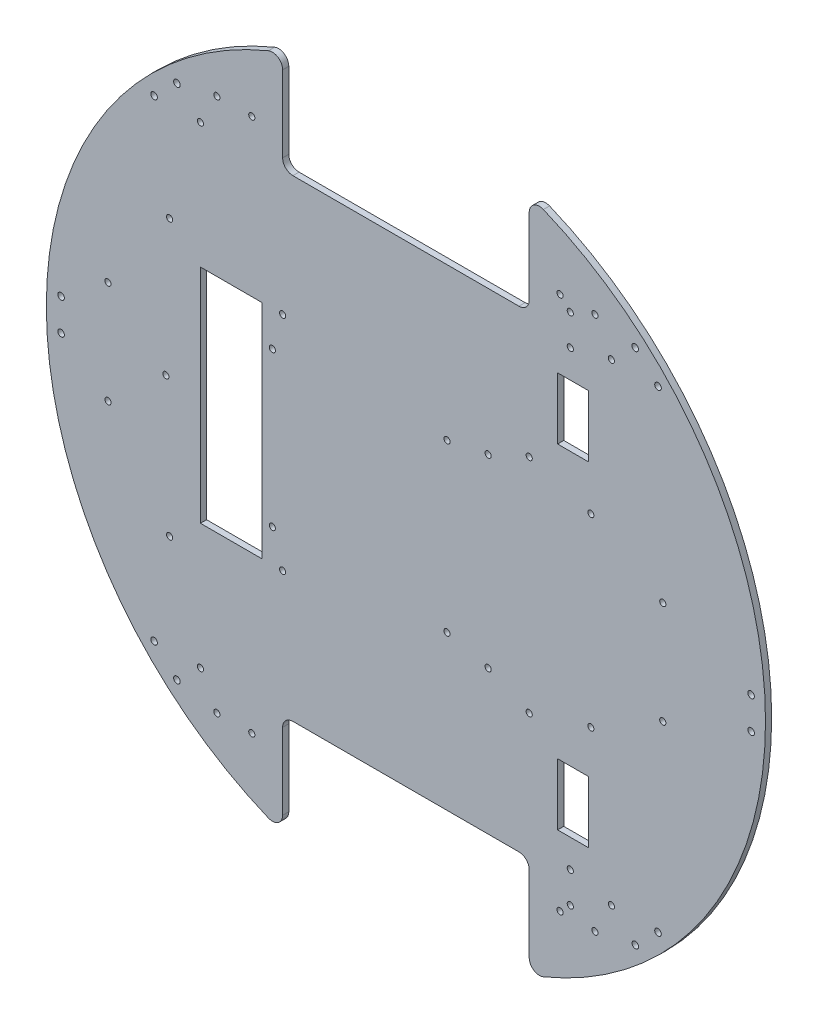
SolidWorks part; units mm, degrees
material "ｱｸﾘﾙ (中-上級の耐衝撃性)"
ref_plane "正面" through (0, 0, 0) normal (0, 0, 1) x (1, 0, 0)
ref_plane "平面" through (0, 0, 0) normal (0, 1, 0) x (1, 0, 0)
ref_plane "右側面" through (0, 0, 0) normal (1, 0, 0) x (0, 0, -1)
sketch "ｽｹｯﾁ1" plane through (0, 0, 0) normal (0, 0, 1) x (1, 0, 0)
  circle A0 centre (0, 0) radius 175
  dimension "D1" = 350
extrude "ﾎﾞｽ - 押し出し1" add sketch "ｽｹｯﾁ1" along normal blind 3
sketch "ｽｹｯﾁ2" plane through (0, 0, 3) normal (0, 0, 1) x (1, 0, 0)
  line L0 (0, 0) -> (175, 0)
  line L1 (0, 0) -> (-175, 0)
  line L2 (0, 0) -> (0, 115)
  line L3 (0, 0) -> (0, -115)
  line L4 (0, 115) -> (60, 115)
  line L5 (0, 115) -> (0, 175)
  line L6 (0, 175) -> (60, 175)
  line L7 (60, 115) -> (60, 175)
  line L8 (0, 115) -> (-60, 115)
  line L9 (0, 115) -> (0, 175)
  line L10 (0, 175) -> (-60, 175)
  line L11 (-60, 115) -> (-60, 175)
  line L13 (0, -115) -> (60, -115)
  line L14 (0, -115) -> (0, -175)
  line L15 (0, -175) -> (60, -175)
  line L16 (60, -115) -> (60, -175)
  line L17 (0, -115) -> (-60, -115)
  line L18 (0, -115) -> (0, -175)
  line L19 (0, -175) -> (-60, -175)
  line L20 (-60, -115) -> (-60, -175)
  circle A0 centre (0, 0) radius 175 construction
  circle M1 centre (0, 0) radius 175
  dimension "D1" = 115
  dimension "D2" = 60
  dimension "D3" = 60
  dimension "D4" = 60
  dimension "D5" = 115
  dimension "D6" = 60
extrude "ｶｯﾄ - 押し出し1" cut sketch "ｽｹｯﾁ2" against normal blind 3 contours L11 L8 L5 M1 | L4 L7 L5 M1 | L17 L20 L14 M1 | L16 L13 L14 M1
fillet "ﾌｨﾚｯﾄ1" radius 5 1 edges at (-60, 164.3928, 1.5)
fillet "ﾌｨﾚｯﾄ2" radius 5 3 edges at (60, 115, 1.5) (60, 164.3928, 1.5) (-60, 115, 1.5)
fillet "ﾌｨﾚｯﾄ3" radius 5 4 edges at (-60, -164.3928, 1.5) (-60, -115, 1.5) (60, -164.3928, 1.5) (60, -115, 1.5)
sketch "ｽｹｯﾁ5" plane through (0, 0, 3) normal (0, 0, 1) x (1, 0, 0)
  line L0 (0, 115) -> (-100, 115)
  line L1 (55, 115) -> (-55, 115) construction
  line L2 (0, 115) -> (100, 115)
  line L3 (0, -115) -> (100, -115)
  line L4 (55, -115) -> (-55, -115) construction
  line L5 (100, -115) -> (-100, -115)
  circle A0 centre (-100, -115) radius 1.5
  circle A1 centre (100, -115) radius 1.5
  circle A2 centre (100, 115) radius 1.5
  circle A3 centre (-100, 115) radius 1.5
  dimension "D3" = 3
  dimension "D4" = 3
  dimension "D5" = 3
  dimension "D6" = 3
  dimension "D1" = 100
  dimension "D2" = 100
extrude "ｶｯﾄ - 押し出し4" cut sketch "ｽｹｯﾁ5" against normal blind 3 contours A1 | A0 | A3 | A2
sketch "ｽｹｯﾁ6" plane through (0, 0, 3) normal (0, 0, 1) x (1, 0, 0)
  line L1 (-60, 54) -> (60, 54)
  line L2 (-60, 54) -> (-60, -54)
  line L3 (-60, -54) -> (60, -54)
  line L4 (60, 54) -> (60, -54)
  line L5 (-60, 54) -> (60, -54) construction
  line L6 (-60, -54) -> (60, 54) construction
  circle A0 centre (-60, 54) radius 1.5
  circle A1 centre (60, 54) radius 1.5
  circle A2 centre (-60, -54) radius 1.5
  circle A3 centre (60, -54) radius 1.5
  point P0 (0, 0)
  dimension "D3" = 3
  dimension "D4" = 3
  dimension "D5" = 3
  dimension "D6" = 3
  dimension "D1" = 120
  dimension "D2" = 108
extrude "ｶｯﾄ - 押し出し5" cut sketch "ｽｹｯﾁ6" against normal blind 3 contours A2 | A0 | A1 | A3
sketch "ｽｹｯﾁ7" plane through (0, 0, 3) normal (0, 0, 1) x (1, 0, 0)
  line L0 (-60, -54) -> (-70, -54)
  line L2 (-70, -54) -> (-100, -54)
  line L3 (-70, -54) -> (-70, 54)
  line L4 (-70, 54) -> (-100, 54)
  line L5 (-100, -54) -> (-100, 54)
  dimension "D1" = 10
  dimension "D2" = 108
  dimension "D3" = 30
extrude "ｶｯﾄ - 押し出し6" cut sketch "ｽｹｯﾁ7" against normal blind 3 contours L5 L2 L3 L4
sketch "ｽｹｯﾁ8" plane through (0, 0, 3) normal (0, 0, 1) x (1, 0, 0)
  line L0 (-100, 0) -> (-115, 0)
  line L1 (-100, -54) -> (-100, 54) construction
  line L2 (-115, 0) -> (-115, 67)
  line L3 (-115, 0) -> (-115, -67)
  circle A0 centre (-115, -67) radius 1.5
  circle A1 centre (-116.8225, 0) radius 1.5
  circle A2 centre (-115, 67) radius 1.5
  dimension "D4" = 3
  dimension "D5" = 3
  dimension "D6" = 3
  dimension "D1" = 15
  dimension "D2" = 67
  dimension "D3" = 67
extrude "ｶｯﾄ - 押し出し7" cut sketch "ｽｹｯﾁ8" against normal blind 3 contours A2 | A1 | A0
sketch "ｽｹｯﾁ9" plane through (0, 0, 3) normal (0, 0, 1) x (1, 0, 0)
  line L0 (-70, 0) -> (-65, 0)
  line L1 (-70, -54) -> (-70, 54) construction
  line L2 (-65, 0) -> (-65, 37)
  line L3 (-65, 37) -> (-64.7716, 37.1905)
  line L4 (-65, 0) -> (-65, -38)
  line L5 (-65, 0) -> (20, 0)
  line L6 (20, 0) -> (20, 41)
  line L7 (20, 0) -> (20, -40)
  circle A0 centre (-65, 37) radius 1.5
  circle A1 centre (20, 41) radius 1.5
  circle A2 centre (-65, -38) radius 1.5
  circle A3 centre (20, -40) radius 1.5
  dimension "D7" = 3
  dimension "D8" = 3
  dimension "D9" = 3
  dimension "D10" = 3
  dimension "D1" = 5
  dimension "D2" = 37
  dimension "D3" = 38
  dimension "D4" = 85
  dimension "D5" = 41
  dimension "D6" = 40
extrude "ｶｯﾄ - 押し出し8" cut sketch "ｽｹｯﾁ9" against normal blind 10 contours A0 | A2 | A1 | A3
sketch "ｽｹｯﾁ10" plane through (0, 0, 3) normal (0, 0, 1) x (1, 0, 0)
  line L0 (0, 0) -> (152.2366, 0)
  line L1 (0, 0) -> (66.9742, 68.8711)
  line L2 (0, 0) -> (76.2283, -78.3873)
  line L3 (175, 0) -> (168, 0)
  line L4 (-175, 0) -> (-168, 0)
  line L5 (66.9742, 68.8711) -> (117.1237, 120.441)
  line L6 (76.2283, -78.3873) -> (117.1237, -120.441)
  line L7 (117.1237, -120.441) -> (122.6798, -115.038)
  line L8 (117.1237, -120.441) -> (111.6437, -125.9211)
  line L9 (168, 0) -> (168, 7.75)
  line L10 (168, 0) -> (168, -7.75)
  line L11 (117.1237, 120.441) -> (111.5677, 125.844)
  line L12 (117.1237, 120.441) -> (122.6798, 115.038)
  line L13 (0, 0) -> (-209.5764, 0)
  arc A0 (66.9118, -161.7029) -> (66.9118, 161.7029) centre (0, 0) ccw construction
  arc A1 (-66.9118, 161.7029) -> (-66.9118, -161.7029) centre (0, 0) ccw construction
  circle A2 centre (0, 0) radius 168
  circle A3 centre (111.6437, -125.9211) radius 1.6
  circle A4 centre (122.6798, -115.038) radius 1.6
  circle A5 centre (168, 7.75) radius 1.6
  circle A6 centre (168, -7.75) radius 1.6
  circle A7 centre (111.5677, 125.844) radius 1.6
  circle A8 centre (122.6798, 115.038) radius 1.6
  dimension "D7" = 3.2
  dimension "D8" = 3.2
  dimension "D11" = 3.2
  dimension "D12" = 3.2
  dimension "D15" = 3.2
  dimension "D16" = 3.2
  dimension "D1" = 45.8
  dimension "D2" = 45.8
  dimension "D3" = 7
  dimension "D4" = 7
  dimension "D5" = 7.75
  dimension "D6" = 7.75
  dimension "D9" = 7.75
  dimension "D10" = 7.75
  dimension "D13" = 7.75
  dimension "D14" = 7.75
extrude "バンパ用 前" cut sketch "ｽｹｯﾁ10" against normal blind 10 contours A3 | A4 | A6 | A5 | A7 | A8
sketch "ｽｹｯﾁ11" plane through (0, 0, 3) normal (0, 0, 1) x (1, 0, 0)
  line L0 (0, 0) -> (115, 0)
  line L1 (0, 0) -> (81.3173, 81.3173)
  line L2 (0, 0) -> (81.3173, -81.3173)
  line L4 (73.8173, 96.3173) -> (88.8173, 96.3173)
  line L5 (73.8173, 96.3173) -> (73.8173, 66.3173)
  line L6 (73.8173, 66.3173) -> (88.8173, 66.3173)
  line L7 (88.8173, 96.3173) -> (88.8173, 66.3173)
  line L8 (73.8173, 96.3173) -> (88.8173, 66.3173) construction
  line L9 (73.8173, 66.3173) -> (88.8173, 96.3173) construction
  line L10 (73.8173, -66.3173) -> (88.8173, -66.3173)
  line L11 (73.8173, -66.3173) -> (73.8173, -96.3173)
  line L12 (73.8173, -96.3173) -> (88.8173, -96.3173)
  line L13 (88.8173, -66.3173) -> (88.8173, -96.3173)
  line L14 (73.8173, -66.3173) -> (88.8173, -96.3173) construction
  line L15 (73.8173, -96.3173) -> (88.8173, -66.3173) construction
  circle A0 centre (0, 0) radius 115
  dimension "D1" = 230
  dimension "D2" = 45
  dimension "D3" = 45
  dimension "D4" = 30
  dimension "D5" = 15
  dimension "D6" = 15
  dimension "D7" = 30
extrude "ｶｯﾄ - 押し出し10" cut sketch "ｽｹｯﾁ11" against normal blind 10 contours L7 L6 L5 L4 | L13 L12 L11 L10
sketch "ｽｹｯﾁ12" plane through (0, 0, 3) normal (0, 0, 1) x (1, 0, 0)
sketch "ｽｹｯﾁ18" plane through (0, 0, 3) normal (0, 0, 1) x (1, 0, 0)
sketch "ｽｹｯﾁ19" plane through (0, 0, 3) normal (0, 0, 1) x (1, 0, 0)
  line L0 (0, 0) -> (-202.6409, 0)
  line L1 (-202.6409, 0) -> (0, 0)
  line L2 (0, 0) -> (-146.7224, 150.8779)
  line L3 (-146.7224, 150.8779) -> (0, 0)
  line L4 (0, 0) -> (-138.2921, -142.2089)
  line L5 (-138.2921, -142.2089) -> (0, 0)
  circle A0 centre (0, 0) radius 168
  arc A1 (-66.9118, 161.7029) -> (-66.9118, -161.7029) centre (0, 0) ccw construction
  circle A2 centre (-111.443, 125.7158) radius 1.6
  circle A3 centre (-122.5551, 114.9097) radius 1.6
  circle A4 centre (-167.8211, 7.75) radius 1.6
  circle A5 centre (-167.8211, -7.75) radius 1.6
  circle A6 centre (-122.5551, -114.9097) radius 1.6
  circle A7 centre (-111.443, -125.7158) radius 1.6
  dimension "D3" = 7
  dimension "D4" = 3.2
  dimension "D7" = 3.2
  dimension "D10" = 3.2
  dimension "D11" = 3.2
  dimension "D14" = 3.2
  dimension "D15" = 3.2
  dimension "D1" = 45.8
  dimension "D2" = 45.8
  dimension "D5" = 7.75
  dimension "D6" = 7.75
  dimension "D8" = 7.75
  dimension "D9" = 7.75
  dimension "D12" = 7.75
  dimension "D13" = 7.75
extrude "バンパ用 後ろ" cut sketch "ｽｹｯﾁ19" against normal blind 10 contours A2 | A3 | A4 | A5 | A6 | A7
sketch "ｽｹｯﾁ21" plane through (0, 0, 3) normal (0, 0, 1) x (1, 0, 0)
  line L0 (0, 0) -> (-188.9986, 0)
  line L1 (-188.9986, 0) -> (203.4492, 0)
  line L2 (203.4492, 0) -> (0, 0)
  line L3 (-175, 0) -> (-175, 65.3253)
  line L4 (-175, 65.3253) -> (-175, -68.6954)
  line L5 (-175, -68.6954) -> (-175, 65.3253)
  arc A0 (-66.9118, 161.7029) -> (-66.9118, -161.7029) centre (0, 0) ccw construction
  circle A1 centre (-145, 25) radius 1.5
  circle A2 centre (-145, -25) radius 1.5
  dimension "D5" = 3
  dimension "D6" = 3
  dimension "D1" = 25
  dimension "D2" = 25
  dimension "D3" = 30
  dimension "D4" = 30
extrude "Webカメラ用後ろ" cut sketch "ｽｹｯﾁ21" against normal blind 10 contours A1 | A2
sketch "ｽｹｯﾁ22" plane through (0, 0, 3) normal (0, 0, 1) x (1, 0, 0)
  line L0 (175, 0) -> (175, 69.7115)
  line L1 (175, 69.7115) -> (175, -66.9063)
  line L2 (175, -66.9063) -> (175, 69.7115)
  line L3 (0, 0) -> (204.143, 0)
  line L4 (204.143, 0) -> (0, 0)
  arc A0 (66.9118, -161.7029) -> (66.9118, 161.7029) centre (0, 0) ccw construction
  circle A1 centre (125, 25) radius 1.5
  circle A2 centre (125, -25) radius 1.5
  dimension "D5" = 3
  dimension "D6" = 3
  dimension "D1" = 25
  dimension "D2" = 25
  dimension "D3" = 50
  dimension "D4" = 50
extrude "Webカメラ用前" cut sketch "ｽｹｯﾁ22" against normal blind 10 contours A1 | A2
sketch "ｽｹｯﾁ23" plane through (0, 0, 3) normal (0, 0, 1) x (1, 0, 0)
sketch "ｽｹｯﾁ28" plane through (0, 0, 3) normal (0, 0, 1) x (1, 0, 0)
  line L0 (0, 0) -> (0, 74.6964)
  line L1 (0, 74.6964) -> (0, -69.9782)
  line L2 (0, -69.9782) -> (0, 74.6964)
  line L3 (0, 0) -> (158.0121, 0)
  line L4 (158.0121, 0) -> (0, 0)
  circle A0 centre (40, 45) radius 1.5
  circle A1 centre (90, 45) radius 1.5
  circle A2 centre (40, -45) radius 1.5
  circle A3 centre (90, -45) radius 1.5
  dimension "D5" = 3
  dimension "D6" = 3
  dimension "D7" = 3
  dimension "D8" = 3
  dimension "D1" = 45
  dimension "D2" = 45
  dimension "D3" = 45
  dimension "D4" = 45
  dimension "D10" = 40
  dimension "D11" = 40
  dimension "D12" = 50
  dimension "D13" = 50
extrude "電源ボード用" cut sketch "ｽｹｯﾁ28" against normal blind 10 contours A0 | A1 | A2 | A3
sketch "ｽｹｯﾁ29" plane through (0, 0, 3) normal (0, 0, 1) x (1, 0, 0)
  line L0 (0, 0) -> (0, 166.2692)
  line L1 (0, 166.2692) -> (0, -165.37)
  line L2 (0, -165.37) -> (0, 166.2692)
  circle A0 centre (80, 125) radius 1.5
  circle A1 centre (80, 110) radius 1.5
  circle A2 centre (80, -110) radius 1.5
  circle A3 centre (80, -125) radius 1.5
  dimension "D1" = 3
  dimension "D2" = 3
  dimension "D3" = 3
  dimension "D4" = 3
  dimension "D5" = 15
  dimension "D6" = 80
  dimension "D7" = 110
  dimension "D8" = 15
  dimension "D9" = 80
  dimension "D10" = 110
extrude "超音波センサ用 標準" cut sketch "ｽｹｯﾁ29" against normal blind 10 contours A0 | A1 | A2 | A3
sketch "ｽｹｯﾁ31" plane through (0, 0, 3) normal (0, 0, 1) x (1, 0, 0)
  circle A0 centre (-92, 130) radius 1.5
  circle A1 centre (-75, 130) radius 1.5
  circle A2 centre (75, 130) radius 1.5
  circle A3 centre (92, 130) radius 1.5
  circle A4 centre (92, -130) radius 1.5
  circle A5 centre (75, -130) radius 1.5
  circle A6 centre (-75, -130) radius 1.5
  circle A7 centre (-92, -130) radius 1.5
  dimension "D13" = 3
  dimension "D14" = 3
  dimension "D15" = 3
  dimension "D16" = 3
  dimension "D17" = 3
  dimension "D18" = 3
  dimension "D19" = 3
  dimension "D20" = 3
  dimension "D1" = 17
  dimension "D2" = 17
  dimension "D3" = 17
  dimension "D4" = 17
  dimension "D5" = 130
  dimension "D6" = 130
  dimension "D7" = 130
  dimension "D8" = 130
  dimension "D9" = 75
  dimension "D10" = 75
  dimension "D11" = 75
  dimension "D12" = 75
extrude "超音波センサ用 市販" cut sketch "ｽｹｯﾁ31" against normal blind 10
equation "\"５０\"=30"
